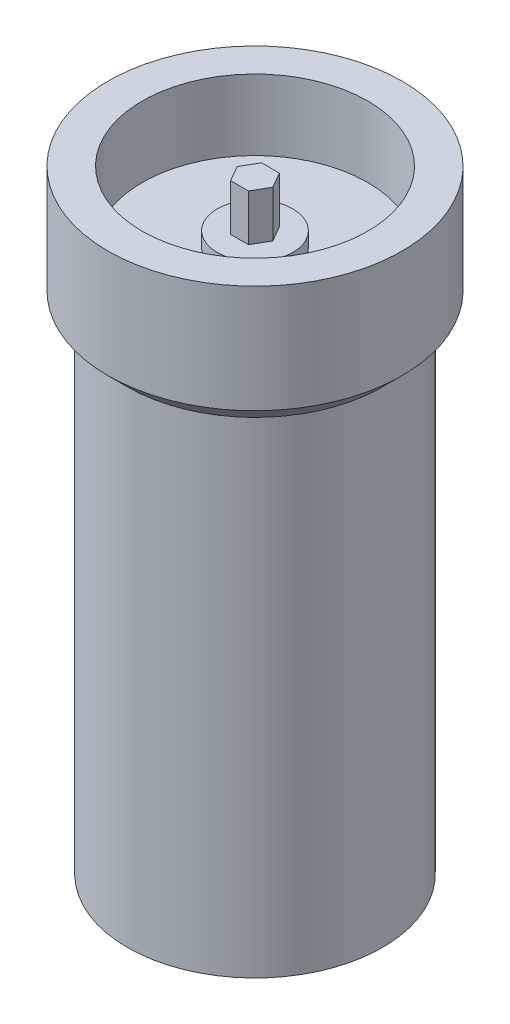
SolidWorks part; units mm, degrees
ref_plane "Front Plane" through (0, 0, 0) normal (0, 0, 1) x (1, 0, 0)
ref_plane "Top Plane" through (0, 0, 0) normal (0, 1, 0) x (1, 0, 0)
ref_plane "Right Plane" through (0, 0, 0) normal (1, 0, 0) x (0, 0, -1)
sketch "Sketch1" plane through (0, 0, 0) normal (0, 0, 1) x (1, 0, 0)
  line L0 (0, 0) -> (0, 125)
  line L1 (0, 125) -> (30, 125)
  line L2 (30, 125) -> (30, 103)
  line L4 (26, 99) -> (26, 0)
  line L5 (26, 0) -> (0, 0)
  line L6 (30, 103) -> (26, 99)
  point P7 (0, 0)
  point P9 (26, 98.856)
  dimension "D1" = 125
  dimension "D2" = 30
  dimension "D3" = 22
  dimension "D4" = 26
  dimension "D5" = 135
revolve "Revolve1" add sketch "Sketch1" angle 360 about L0
sketch "Sketch2" plane through (0, 125, 0) normal (0, 1, 0) x (1, 0, 0)
  circle A0 centre (0, 0) radius 23
  dimension "D1" = 46
extrude "Cut-Extrude1" cut sketch "Sketch2" against normal blind 14.4
sketch "Sketch3" plane through (0, 110.6, 0) normal (0, 1, 0) x (1, 0, 0)
  line L1 (3.6373, 0) -> (1.8187, 3.15)
  line L2 (1.8187, 3.15) -> (-1.8187, 3.15)
  line L3 (-1.8187, 3.15) -> (-3.6373, 0)
  line L4 (-3.6373, 0) -> (-1.8187, -3.15)
  line L5 (-1.8187, -3.15) -> (1.8187, -3.15)
  line L6 (1.8187, -3.15) -> (3.6373, 0)
  circle A0 centre (0, 0) radius 3.15 construction
extrude "Boss-Extrude1" add sketch "Sketch3" along normal blind 12.5 separate body
sketch "Sketch4" plane through (0, 110.6, 0) normal (0, 1, 0) x (1, 0, 0)
  circle A0 centre (0, 0) radius 7.7
  dimension "D1" = 15.4
extrude "Boss-Extrude2" add sketch "Sketch4" along normal blind 3 separate body
